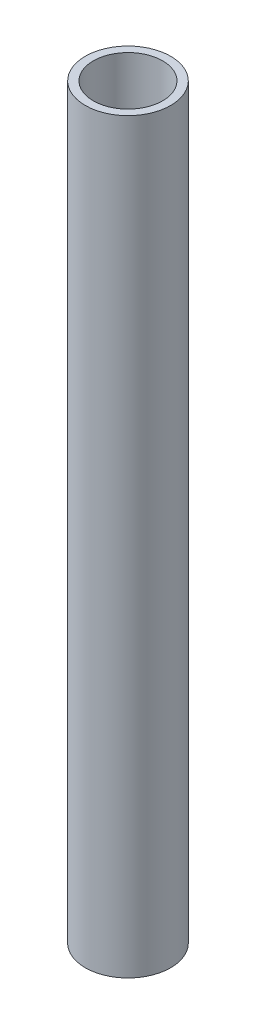
SolidWorks part; units mm, degrees
material "PVC Rígido"
ref_plane "Alzado" through (0, 0, 0) normal (0, 0, 1) x (1, 0, 0)
ref_plane "Planta" through (0, 0, 0) normal (0, 1, 0) x (1, 0, 0)
ref_plane "Vista lateral" through (0, 0, 0) normal (1, 0, 0) x (0, 0, -1)
sketch "Croquis1" plane through (0, 0, 0) normal (0, 1, 0) x (1, 0, 0)
  circle A0 centre (0, 0) radius 6.5
  circle A1 centre (0, 0) radius 8
  dimension "D1" = 13
  dimension "D2" = 16
extrude "Saliente-Extruir1" add sketch "Croquis1" along normal blind 140
